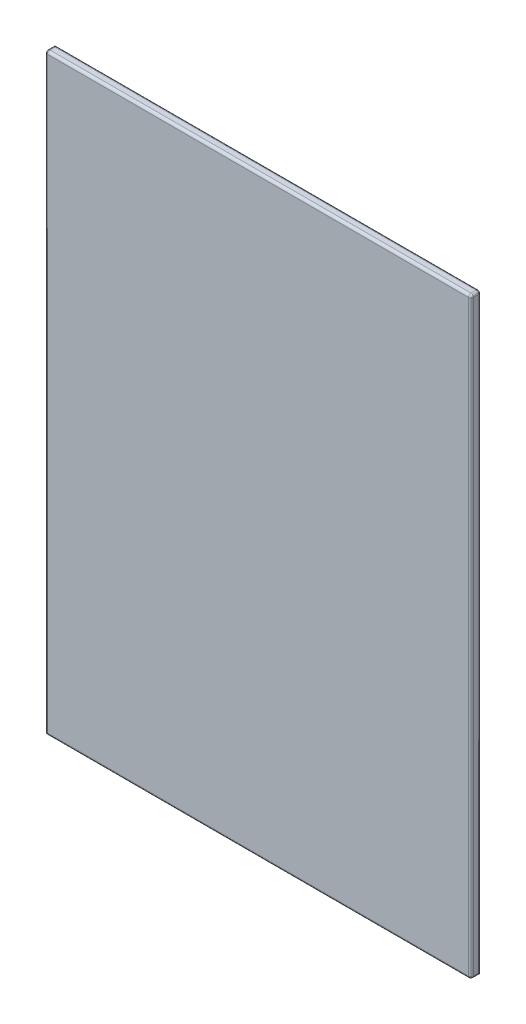
SolidWorks part; units mm, degrees
material "Acrylic (Medium-high impact)"
ref_plane "Front Plane" through (0, 0, 0) normal (0, 0, 1) x (1, 0, 0)
ref_plane "Top Plane" through (0, 0, 0) normal (0, 1, 0) x (1, 0, 0)
ref_plane "Right Plane" through (0, 0, 0) normal (1, 0, 0) x (0, 0, -1)
sketch "Sketch1" plane through (0, 0, 0) normal (0, 0, 1) x (1, 0, 0)
  line L1 (-427.5, 595) -> (427.5, 595)
  line L2 (-427.5, 595) -> (-427.5, -595)
  line L3 (-427.5, -595) -> (427.5, -595)
  line L4 (427.5, 595) -> (427.5, -595)
  line L5 (-427.5, 595) -> (427.5, -595) construction
  line L6 (-427.5, -595) -> (427.5, 595) construction
  point P0 (0, 0)
  dimension "D1" = 855
  dimension "D2" = 1190
extrude "Boss-Extrude1" add sketch "Sketch1" along normal blind 20
fillet "Fillet1" radius 5 9 edges at (427.5, 0, 0) (0, 595, 0) (427.5, 0, 20) (0, 595, 20) (-427.5, 0, 20) (0, -595, 20) (427.5, -595, 10) (-427.5, 595, 10) (427.5, 595, 10)
